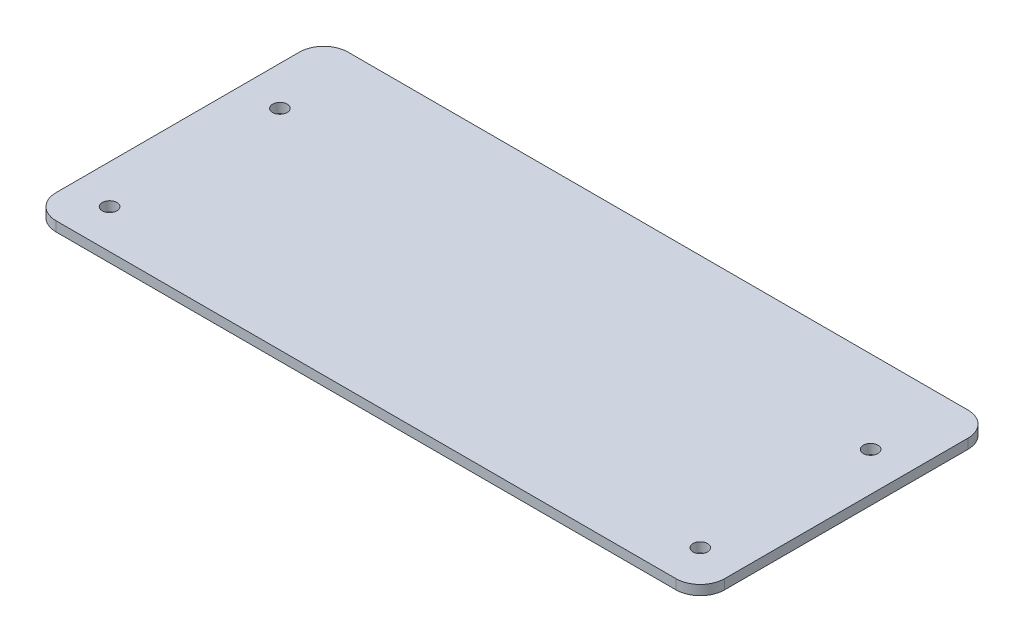
SolidWorks part; units mm, degrees
ref_plane "Front Plane" through (0, 0, 0) normal (0, 0, 1) x (1, 0, 0)
ref_plane "Top Plane" through (0, 0, 0) normal (0, 1, 0) x (1, 0, 0)
ref_plane "Right Plane" through (0, 0, 0) normal (1, 0, 0) x (0, 0, -1)
sketch "Sketch1" plane through (0, 0, 0) normal (0, 1, 0) x (1, 0, 0)
  line L1 (-687.3009, 62.6442) -> (-814.6609, 62.6442)
  line L2 (-682.3009, 57.6442) -> (-682.3009, 7.6442)
  line L3 (-687.3009, 2.6442) -> (-814.6609, 2.6442)
  line L4 (-819.6609, 57.6442) -> (-819.6609, 7.6442)
  line L5 (-819.6609, 81.9442) -> (-819.6609, 14.6442) construction
  arc A0 (-682.3009, 57.6442) -> (-687.3009, 62.6442) centre (-687.3009, 57.6442) ccw
  arc A1 (-682.3009, 7.6442) -> (-687.3009, 2.6442) centre (-687.3009, 7.6442) cw
  arc A2 (-814.6609, 2.6442) -> (-819.6609, 7.6442) centre (-814.6609, 7.6442) cw
  arc A3 (-819.6609, 57.6442) -> (-814.6609, 62.6442) centre (-814.6609, 57.6442) cw
  point P6 (-682.3009, 62.6442)
  point P11 (-819.6609, 2.6442)
  point P14 (-819.6609, 62.6442)
  dimension "D3" = 5
  dimension "D1" = 137.36
  dimension "D2" = 60
  dimension "D4" = 0
extrude "Boss-Extrude1" add sketch "Sketch1" along normal blind 2
sketch "Sketch4" plane through (0, 0, 0) normal (0, -1, 0) x (1, 0, 0)
  line L0 (-814.6609, -2.6442) -> (-687.3009, -2.6442) construction
  line L1 (-819.6609, -57.6442) -> (-819.6609, -7.6442) construction
  circle A0 centre (-811.6609, -10.6442) radius 1.5
  circle A1 centre (-811.6609, -45.6442) radius 1.5
  circle A2 centre (-690.3009, -10.6442) radius 1.5
  circle A3 centre (-690.3009, -45.6442) radius 1.5
  dimension "D1" = 3
  dimension "D2" = 3
  dimension "D3" = 3
  dimension "D4" = 3
  dimension "D5" = 8
  dimension "D6" = 8
  dimension "D7" = 35
  dimension "D8" = 35
  dimension "D9" = 121.36
  dimension "D10" = 121.36
  dimension "D11" = 8
  dimension "D12" = 8
extrude "Cut-Extrude1" cut sketch "Sketch4" against normal through all
